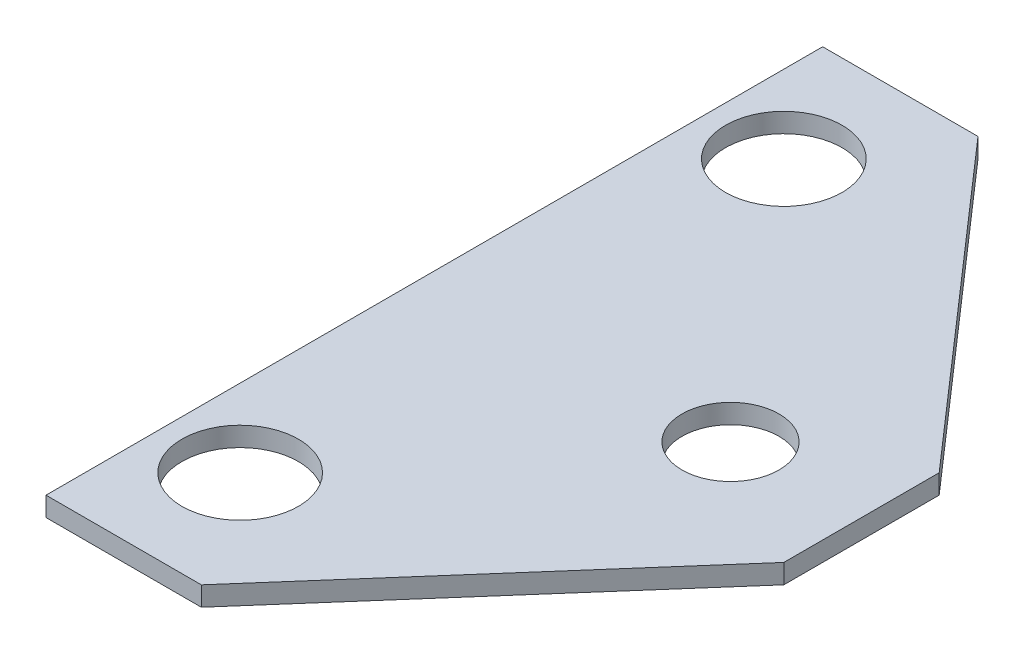
SolidWorks part; units mm, degrees
ref_plane "Front Plane" through (0, 0, 0) normal (0, 0, 1) x (1, 0, 0)
ref_plane "Top Plane" through (0, 0, 0) normal (0, 1, 0) x (1, 0, 0)
ref_plane "Right Plane" through (0, 0, 0) normal (1, 0, 0) x (0, 0, -1)
sketch "Sketch1" plane through (0, 0, 0) normal (0, 1, 0) x (1, 0, 0)
  line L0 (-0.5916, 16.5331) -> (-0.5916, -3.4669)
  line L1 (-0.5916, -3.4669) -> (3.4084, -3.4669)
  line L2 (10.4084, 6.5331) -> (10.4084, 8.5331)
  line L3 (10.4084, 6.5331) -> (10.4084, 4.5331)
  line L4 (3.4084, 16.5331) -> (10.4084, 8.5331)
  line L5 (3.4084, 16.5331) -> (-0.5916, 16.5331)
  line L6 (-0.5916, 6.5331) -> (10.4084, 6.5331) construction
  line L7 (3.4084, -3.4669) -> (10.4084, 4.5331)
  dimension "D1" = 2
  dimension "D2" = 4
  dimension "D3" = 4
  dimension "D4" = 2
  dimension "D5" = 20
  dimension "D6" = 20
  dimension "D7" = 11
extrude "Boss-Extrude1" add sketch "Sketch1" along normal blind 0.5
sketch "Sketch5" plane through (0, 0.5, 0) normal (0, 1, 0) x (1, 0, 0)
  line L0 (-0.5916, 16.5331) -> (-0.5916, 13.5331) construction
  line L1 (-0.5916, 16.5331) -> (-0.5916, -3.4669) construction
  line L2 (-0.5916, 13.5331) -> (1.4084, 13.5331) construction
  line L3 (-0.5916, -3.4669) -> (-0.5916, -0.4669) construction
  line L4 (-0.5916, -0.4669) -> (1.4084, -0.4669) construction
  dimension "D1" = 3
  dimension "D2" = 2
  dimension "D3" = 2
  dimension "D4" = 3
hole_wizard "Ø3.0mm Dowel Hole1" positions "3DSketch2" profile "Sketch7" hole size "Ø3.0" standard "ISO"
sketch3d "3DSketch2"
  point P0 (1.4084, 0.5, -13.5331)
  point P3 (1.4084, 0.5, 0.4669)
sketch "Sketch7" plane through (1.4084, 0.5, -13.5331) normal (1, 0, 0) x (0, 0, 1)
  line L0 (0, 0) -> (0, 13.6513)
  line L1 (0, 13.6513) -> (1.5, 12.75)
  line L2 (1.5, 12.75) -> (1.5, 0)
  line L5 (1.5, 0) -> (0, 0)
  line L10 (0, 13.6513) -> (-1.5, 12.75) construction
  line L11 (0, -6.35) -> (0, 107.95) construction
  dimension "Hole Dia." = 3
  dimension "Hole Depth" = 12.75
  dimension "Drill Angle" = 118
sketch "Sketch9" plane through (0, 0, 0) normal (0, -1, 0) x (-1, 0, 0)
  line L0 (-10.4084, 6.5331) -> (-7.0349, 6.5331) construction
  line L1 (-10.4084, 4.5331) -> (-10.4084, 8.5331) construction
hole_wizard "M3 Tapped Hole2" positions "3DSketch4" profile "Sketch11" tap size "M3" standard "ISO"
sketch3d "3DSketch4"
  point P0 (7.0349, 0, -6.5331)
sketch "Sketch11" plane through (7.0349, 0, -6.5331) normal (1, 0, 0) x (0, 0, -1)
  line L0 (0, 0) -> (0, 8.2511)
  line L1 (0, 8.2511) -> (1.25, 7.5)
  line L2 (1.25, 7.5) -> (1.25, 0)
  line L5 (1.25, 0) -> (0, 0)
  line L10 (0, 8.2511) -> (-1.25, 7.5) construction
  line L11 (0, -6.35) -> (0, 107.95) construction
  dimension "Tap Drill Dia." = 2.5
  dimension "Tap Drill Depth" = 7.5
  dimension "Drill Angle" = 118
cosmetic thread "Hole Thread3" parameters "D1"=0.5, "D2"=3
